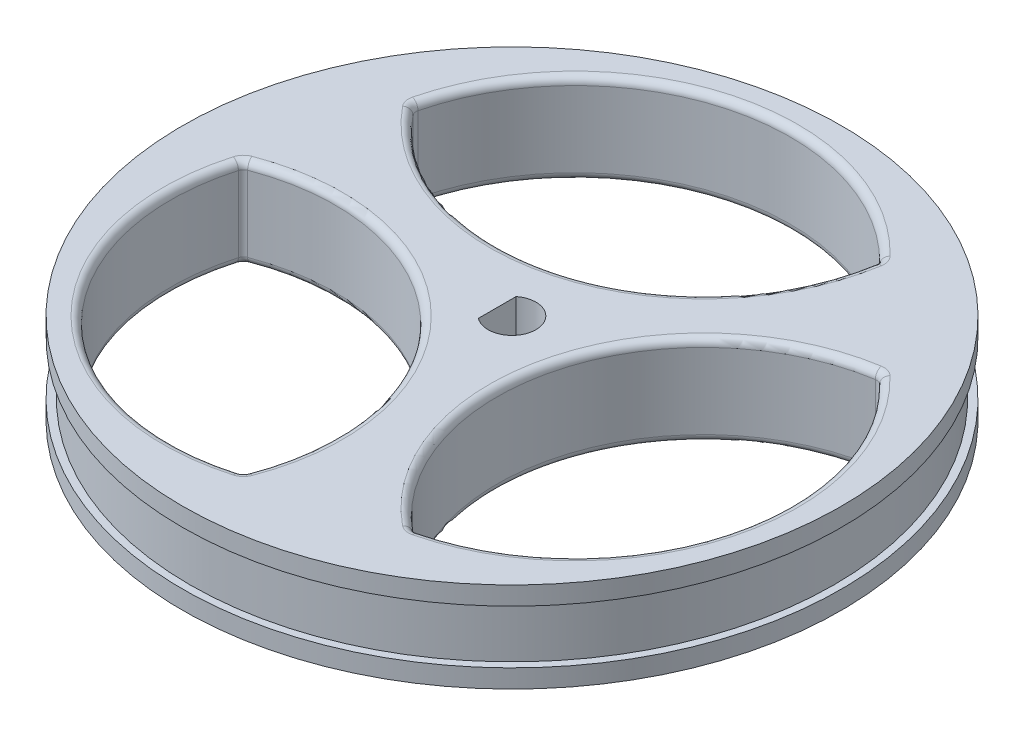
SolidWorks part; units mm, degrees
ref_plane "Front Plane" through (0, 0, 0) normal (0, 0, 1) x (1, 0, 0)
ref_plane "Top Plane" through (0, 0, 0) normal (0, 1, 0) x (1, 0, 0)
ref_plane "Right Plane" through (0, 0, 0) normal (1, 0, 0) x (0, 0, -1)
sketch "Sketch2" plane through (0, 0, 0) normal (0, 1, 0) x (1, 0, 0)
  circle A1 centre (0, 0) radius 22.225
  dimension "D1" = 44.45
extrude "Boss-Extrude1" add sketch "Sketch2" along normal blind 3.683
sketch "Sketch3" plane through (0, 3.683, 0) normal (0, 1, 0) x (1, 0, 0)
  circle A0 centre (0, 0) radius 22.733
  dimension "D1" = 45.466
extrude "Boss-Extrude2" add sketch "Sketch3" along normal blind 1.27
sketch "Sketch4" plane through (0, 0, 0) normal (0, -1, 0) x (-1, 0, 0)
  circle A0 centre (0, 0) radius 22.733
  dimension "D1" = 45.466
extrude "Boss-Extrude3" add sketch "Sketch4" along normal blind 1.27
sketch "Sketch5" plane through (0, -1.27, 0) normal (0, -1, 0) x (1, 0, 0)
  line L0 (1.651, 0) -> (-1.016, 0) construction
  line L1 (-1.016, 1.3014) -> (-1.016, -1.3014) construction
  line L2 (-1.016, 1.3014) -> (-1.016, -1.3014)
  circle A0 centre (0, 0) radius 1.651 construction
  arc A1 (-1.016, -1.3014) -> (-1.016, 1.3014) centre (0, 0) ccw
  dimension "D1" = 3.302
  dimension "D2" = 2.667
extrude "Cut-Extrude1" cut sketch "Sketch5" against normal through all
sketch "Sketch9" plane through (0, -1.27, 0) normal (0, -1, 0) x (-1, 0, 0)
  arc A0 (18.5622, 0) -> (0, -18.5568) centre (4.3447, -4.3405) cw
  arc A1 (18.5622, 0) -> (0, -18.5568) centre (13.2315, -13.23) ccw
extrude "Cut-Extrude3" cut sketch "Sketch9" against normal through all
fillet "Fillet5" radius 0.508 6 edges at (-14.8545, 4.953, 14.8535) (-14.8545, -1.27, 14.8535) (0, 1.8415, 18.5568) (-18.5622, 1.8415, 0) (-3.1472, 4.953, 3.1426) (-3.1472, -1.27, 3.1426)
pattern_circular "CirPattern3" count 3 over 360 about axis through (0, 0, 0) along (0, 1, 0) of "Cut-Extrude3", "Fillet5"
